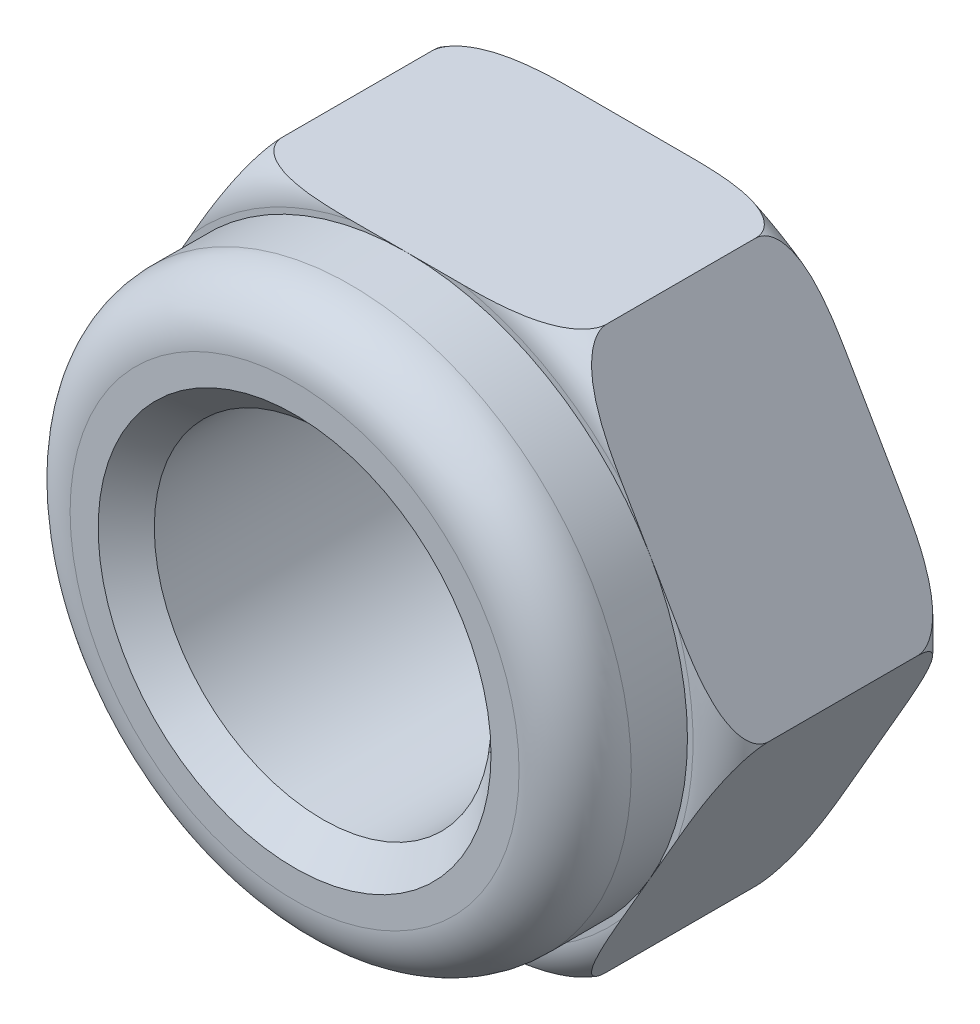
SolidWorks part; units mm, degrees
material "Stal węglowa"
ref_plane "Płaszczyzna XY" through (0, 0, 0) normal (0, 0, 1) x (1, 0, 0)
ref_plane "Płaszczyzna XZ" through (0, 0, 0) normal (0, 1, 0) x (1, 0, 0)
ref_plane "Płaszczyzna YZ" through (0, 0, 0) normal (1, 0, 0) x (0, 0, -1)
sketch "Szkic1" plane through (0, 0, 0) normal (0, 0, 1) x (1, 0, 0)
  line L1 (-5.7735, 0) -> (-2.8868, -5)
  line L2 (-2.8868, -5) -> (2.8868, -5)
  line L3 (2.8868, -5) -> (5.7735, 0)
  line L4 (5.7735, 0) -> (2.8868, 5)
  line L5 (2.8868, 5) -> (-2.8868, 5)
  line L6 (-2.8868, 5) -> (-5.7735, 0)
  circle A0 centre (0, 0) radius 5 construction
  circle A1 centre (0, 0) radius 3
  dimension "d" = 6
  dimension "s" = 10
extrude "Dodanie-wyciągnięcie1" add sketch "Szkic1" along normal blind 4
sketch "Szkic2" plane through (0, 0, 0) normal (0, 0, 1) x (1, 0, 0)
  line L0 (-2.8868, 5) -> (-5.7735, 0) construction
  circle A0 centre (0, 0) radius 3
  circle A1 centre (0, 0) radius 5
  circle A2 centre (0, 0) radius 3 construction
extrude "Dodanie-wyciągnięcie2" add sketch "Szkic2" along normal blind 6
chamfer "Sfazowanie1" distance 0.5 angle 45 2 edges at (3, 0, 6) (3, 0, 0)
sketch "Szkic3" plane through (0, 0, 0) normal (0, 1, 0) x (1, 0, 0)
  line L0 (-5.7735, -0.6735) -> (-5.7735, -3.3265)
  line L1 (-5.1, -4) -> (-2.8868, -4)
  line L2 (-5.1, 0) -> (-2.8868, 0)
  line L3 (0, 1.7016) -> (0, -9.3871) construction
  line L4 (-2.8868, -4) -> (-2.8868, 0)
  line L5 (-5.1, 0) -> (-5.7735, 0)
  line L6 (-5.7735, 0) -> (-5.7735, -4)
  line L7 (-5.7735, -4) -> (-5.1, -4)
  line L8 (-5, -4) -> (-4.3301, -4) construction
  line L9 (-5, -6) -> (5, -6) construction
  line L10 (-5.7735, -4) -> (-4.3301, -4) construction
  line L11 (-5, -4) -> (-5, -6) construction
  line L12 (-5, -4) -> (-5, -6) construction
  line L13 (-5, -5) -> (-5, -6)
  line L14 (-5, -6) -> (-4, -6)
  arc A0 (-5.7735, -3.3265) -> (-5.1, -4) centre (-5.1, -3.3265) ccw
  arc A1 (-5.7735, -0.6735) -> (-5.1, 0) centre (-5.1, -0.6735) cw
  arc A2 (-4, -6) -> (-5, -5) centre (-4, -5) cw
  point P13 (-5.7735, -4)
  point P16 (-5.7735, 0)
  dimension "D1" = 0.1
  dimension "D2" = 0.5
revolve "Wycięcie-obrót1" cut sketch "Szkic3" angle 360 about L3
equation "\"d\"=5"
